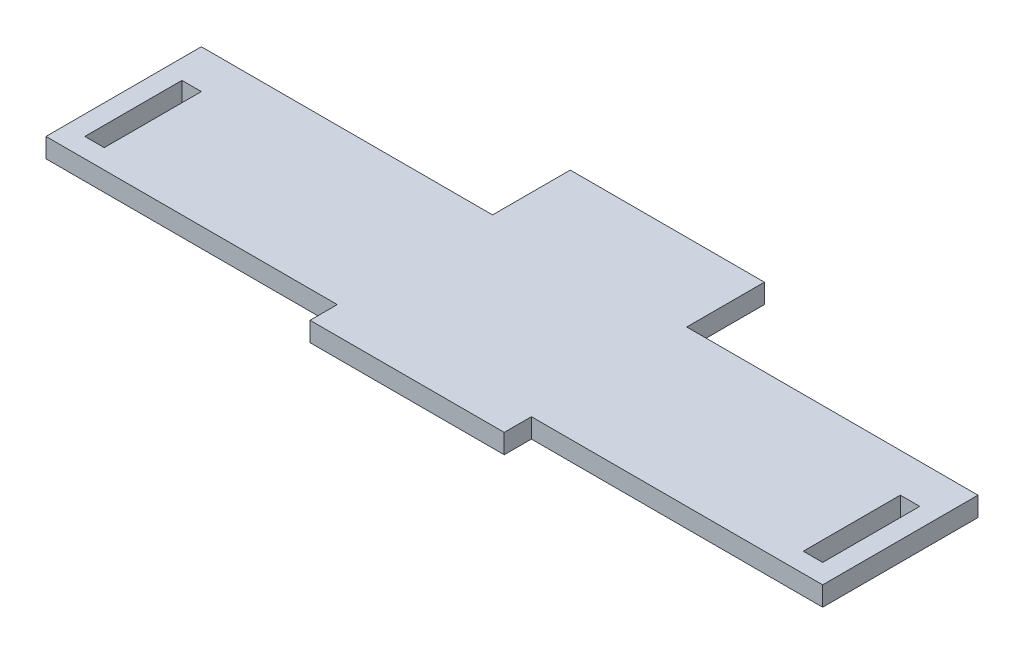
SolidWorks part; units mm, degrees
ref_plane "Front Plane" through (0, 0, 0) normal (0, 0, 1) x (1, 0, 0)
ref_plane "Top Plane" through (0, 0, 0) normal (0, 1, 0) x (1, 0, 0)
ref_plane "Right Plane" through (0, 0, 0) normal (1, 0, 0) x (0, 0, -1)
sketch "Sketch1" plane through (0, 0, 0) normal (0, 1, 0) x (1, 0, 0)
  line L0 (-25, 28.75) -> (-100, 28.75)
  line L1 (-25, -18.25) -> (25, -18.25)
  line L7 (90, -6.25) -> (95, -6.25)
  line L8 (90, -6.25) -> (90, 18.75)
  line L9 (90, 18.75) -> (95, 18.75)
  line L10 (95, -6.25) -> (95, 18.75)
  line L11 (90, -6.25) -> (95, 18.75) construction
  line L12 (90, 18.75) -> (95, -6.25) construction
  line L13 (-90, 18.75) -> (-95, 18.75)
  line L14 (-95, -6.25) -> (-95, 18.75)
  line L15 (-90, -6.25) -> (-95, -6.25)
  line L16 (-90, -6.25) -> (-90, 18.75)
  line L17 (-25, -11.25) -> (-100, -11.25)
  line L18 (-25, -18.25) -> (25, -18.25)
  line L19 (-25, -18.25) -> (-25, -11.25)
  line L21 (25, -18.25) -> (25, -11.25)
  line L24 (25, -11.25) -> (100, -11.25)
  line L27 (-100, 28.75) -> (-100, -11.25)
  line L28 (100, 28.75) -> (100, -11.25)
  line L30 (25, 28.75) -> (100, 28.75)
  line L32 (-25, 28.75) -> (-25, 48.75)
  line L33 (-25, 48.75) -> (25, 48.75)
  line L34 (25, 48.75) -> (25, 28.75)
  point P6 (92.5, 6.25)
  dimension "D3" = 50
  dimension "D4" = 5
  dimension "D6" = 25
  dimension "D7" = 7
  dimension "D8" = 50
  dimension "D11" = 5
  dimension "D13" = 25
  dimension "D15" = 20
extrude "Boss-Extrude1" add sketch "Sketch1" along normal blind 5
